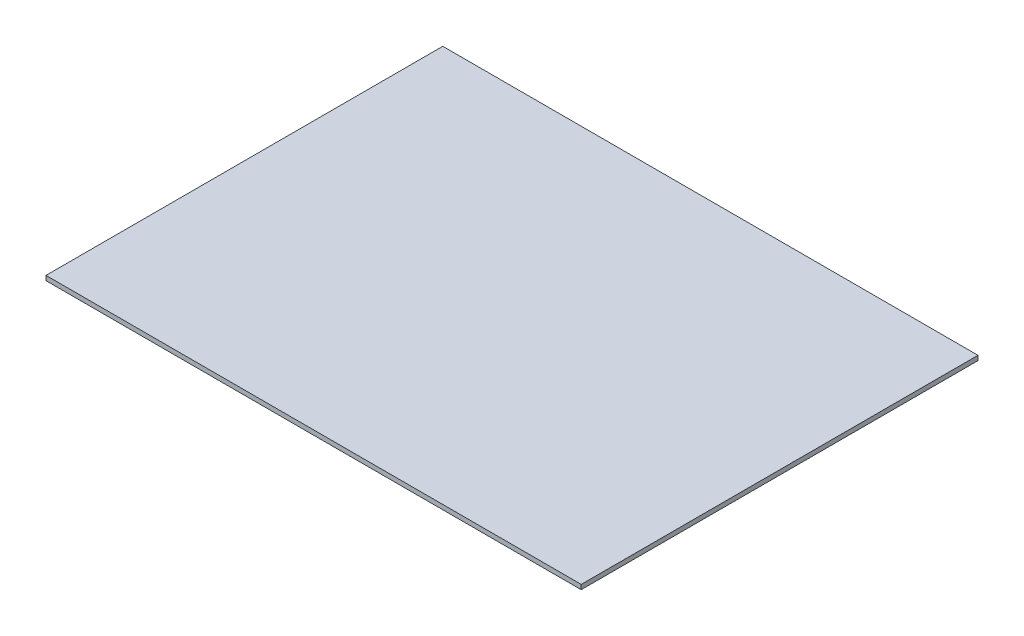
SolidWorks part; units mm, degrees
material "Vidrio"
ref_plane "Alzado" through (0, 0, 0) normal (0, 0, 1) x (1, 0, 0)
ref_plane "Planta" through (0, 0, 0) normal (0, 1, 0) x (1, 0, 0)
ref_plane "Vista lateral" through (0, 0, 0) normal (1, 0, 0) x (0, 0, -1)
sketch "Croquis1" plane through (0, 0, 0) normal (0, 1, 0) x (1, 0, 0)
  line L1 (0, 0) -> (348, 0)
  line L2 (0, 0) -> (0, 258)
  line L3 (0, 258) -> (348, 258)
  line L4 (348, 0) -> (348, 258)
  dimension "D1" = 348
  dimension "D2" = 258
extrude "Saliente-Extruir1" add sketch "Croquis1" along normal blind 3
